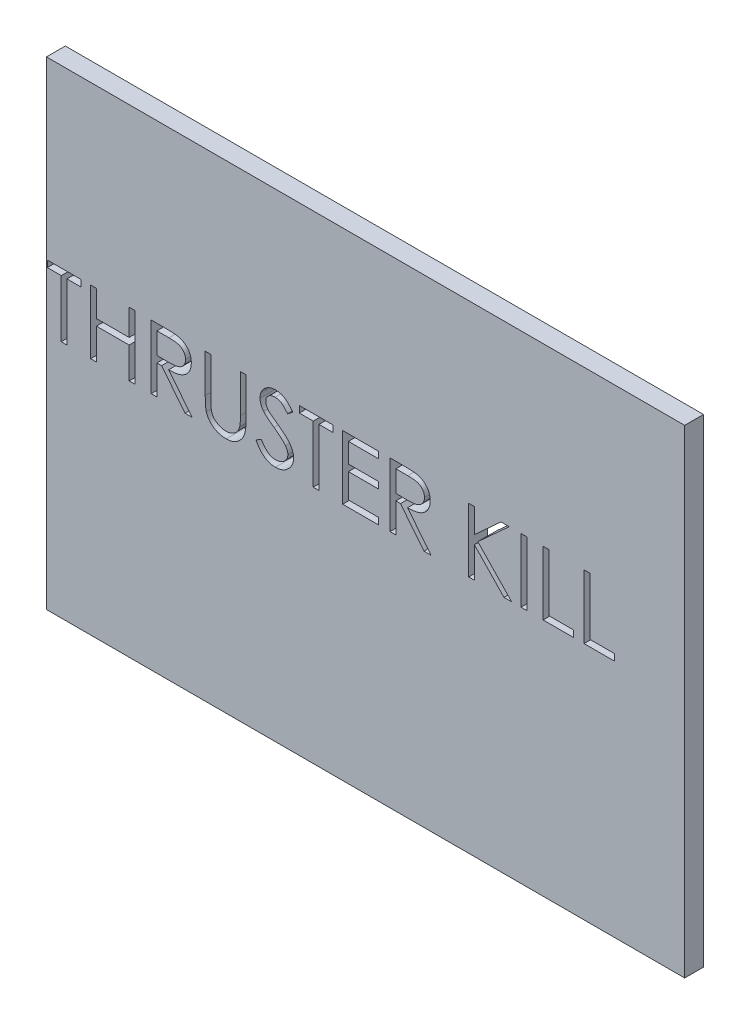
SolidWorks part; units mm, degrees
ref_plane "Front Plane" through (0, 0, 0) normal (0, 0, 1) x (1, 0, 0)
ref_plane "Top Plane" through (0, 0, 0) normal (0, 1, 0) x (1, 0, 0)
ref_plane "Right Plane" through (0, 0, 0) normal (1, 0, 0) x (0, 0, -1)
sketch "Sketch1" plane through (0, 0, 0) normal (0, 0, 1) x (1, 0, 0)
  line L1 (-50.8, 38.1) -> (50.8, 38.1)
  line L2 (-50.8, 38.1) -> (-50.8, -38.1)
  line L3 (-50.8, -38.1) -> (50.8, -38.1)
  line L4 (50.8, 38.1) -> (50.8, -38.1)
  line L5 (-50.8, 38.1) -> (50.8, -38.1) construction
  line L6 (-50.8, -38.1) -> (50.8, 38.1) construction
  point P0 (0, 0)
  dimension "D1" = 101.6
  dimension "D2" = 76.2
extrude "Boss-Extrude1" add sketch "Sketch1" along normal blind 3
sketch "Sketch2" plane through (0, 0, 3) normal (0, 0, 1) x (1, 0, 0)
  line L0 (-50.8, 0) -> (50.8, 0) construction
  line L1 (-50.8, 38.1) -> (-50.8, -38.1) construction
  line L2 (50.8, -38.1) -> (50.8, 38.1) construction
  text T0 "THRUSTER KILL" font "Century Gothic" height 10.16
extrude "Cut-Extrude1" cut sketch "Sketch2" against normal through all both and the other way through all
